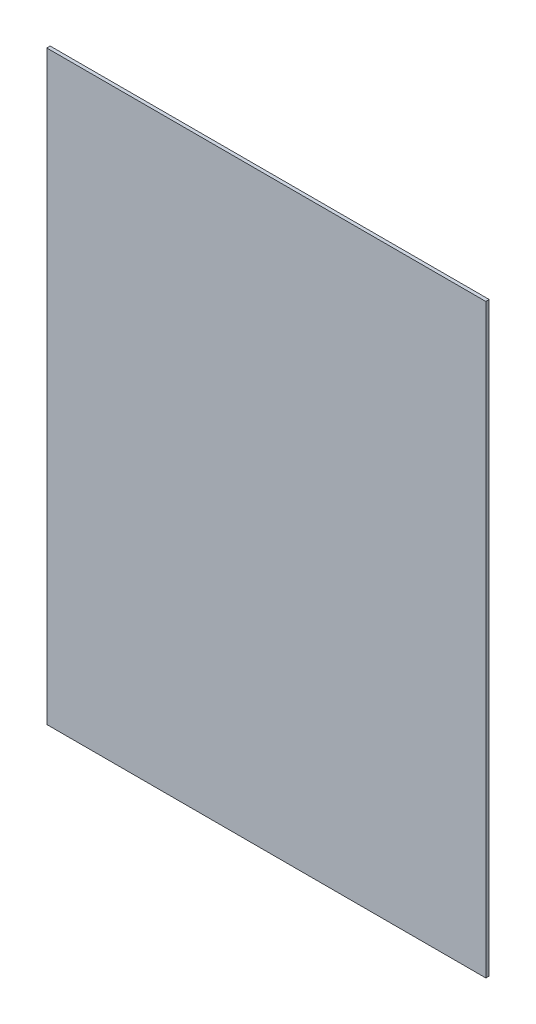
SolidWorks part; units mm, degrees
material "Neoprene Foam"
ref_plane "Front Plane" through (0, 0, 0) normal (0, 0, 1) x (1, 0, 0)
ref_plane "Top Plane" through (0, 0, 0) normal (0, 1, 0) x (1, 0, 0)
ref_plane "Right Plane" through (0, 0, 0) normal (1, 0, 0) x (0, 0, -1)
sketch "Sketch1" plane through (0, 0, 0) normal (0, 0, 1) x (1, 0, 0)
  line L1 (-77, -102.75) -> (77, -102.75)
  line L2 (-77, -102.75) -> (-77, 102.75)
  line L3 (-77, 102.75) -> (77, 102.75)
  line L4 (77, -102.75) -> (77, 102.75)
  line L5 (-77, -102.75) -> (77, 102.75) construction
  line L6 (-77, 102.75) -> (77, -102.75) construction
  point P6 (0, 0)
  dimension "D1" = 154
  dimension "D2" = 205.5
extrude "Body" add sketch "Sketch1" along normal blind 1.1906
